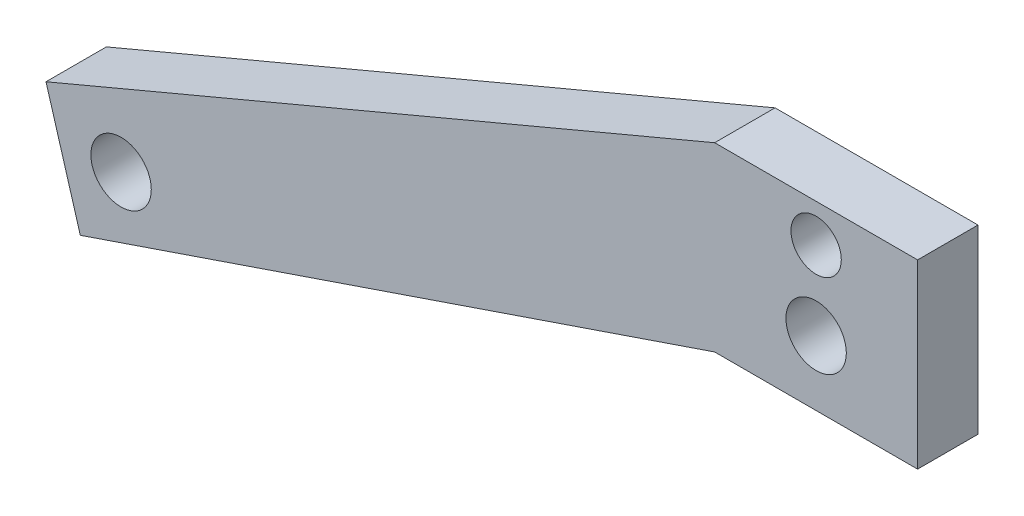
SolidWorks part; units mm, degrees
ref_plane "Front Plane" through (0, 0, 0) normal (0, 0, 1) x (1, 0, 0)
ref_plane "Top Plane" through (0, 0, 0) normal (0, 1, 0) x (1, 0, 0)
ref_plane "Right Plane" through (0, 0, 0) normal (1, 0, 0) x (0, 0, -1)
sketch "Sketch1" plane through (0, 0, 0) normal (0, 0, 1) x (1, 0, 0)
  line L0 (-16, 45) -> (-121.4311, 0.6121)
  line L2 (-276.788, -13.7826) -> (-251.7789, -35.3348) construction
  line L3 (0, 26.6476) -> (-109.5931, -5.8154) construction
  line L4 (-16, 45) -> (-16, 15)
  line L5 (-16, 15) -> (16, 15)
  line L6 (16, 15) -> (16, 45)
  line L7 (16, 45) -> (-16, 45)
  line L8 (-16, 45) -> (-16, 16.425) construction
  line L9 (-16, 15) -> (16, 15) construction
  line L10 (16, 16.425) -> (16, 45)
  line L11 (16, 45) -> (-16, 45)
  line L12 (16, 16.425) -> (-16, 16.425)
  line L13 (-16, 16.425) -> (-116.0206, -17.6534)
  line L14 (-116.0206, -17.6534) -> (-121.4311, 0.6121)
  line L15 (-251.7789, -35.3348) -> (-242.2031, -37.4927) construction
  line L17 (-21.8896, 28.3932) -> (-31.4939, 26.7) construction
  line L18 (-2120.6129, -341.6) -> (-31.4939, 26.7) construction
  line L19 (-242.2031, -37.4927) -> (-208.8903, -37.4927) construction
  line L20 (-208.8903, -37.4927) -> (-16, 45) construction
  line L21 (-292.5067, -43.5335) -> (-248.9466, -55.1606) construction
  line L22 (-248.9466, -55.1606) -> (-208.8903, -56.2396) construction
  line L23 (-208.8903, -56.2396) -> (-14.9476, 16.425) construction
  line L24 (-288.0555, -26.8574) -> (0, 26.6476) construction
  line L47 (-109.5931, -5.8154) -> (-118.7259, -8.5206) construction
  circle A0 centre (0, 39) radius 3.9687 construction
  circle A1 centre (0, 39) radius 3.9688
  circle A2 centre (0, 26.6476) radius 4.7625
  circle A3 centre (-109.5931, -5.8154) radius 4.7625
  circle A4 centre (-288.0555, -26.8574) radius 17.26 construction
  point P21 (-118.7259, -8.5206)
  dimension "D2" = 9.525
  dimension "D4" = 114.3
  dimension "D7" = 292.9825
  dimension "D3" = 9.525
  dimension "D5" = 19.05
  dimension "D6" = 28.575
  dimension "D8" = 106.5
  dimension "D9" = 32
  dimension "D1" = 0
extrude "Boss-Extrude1" add sketch "Sketch1" along normal blind 9.525
